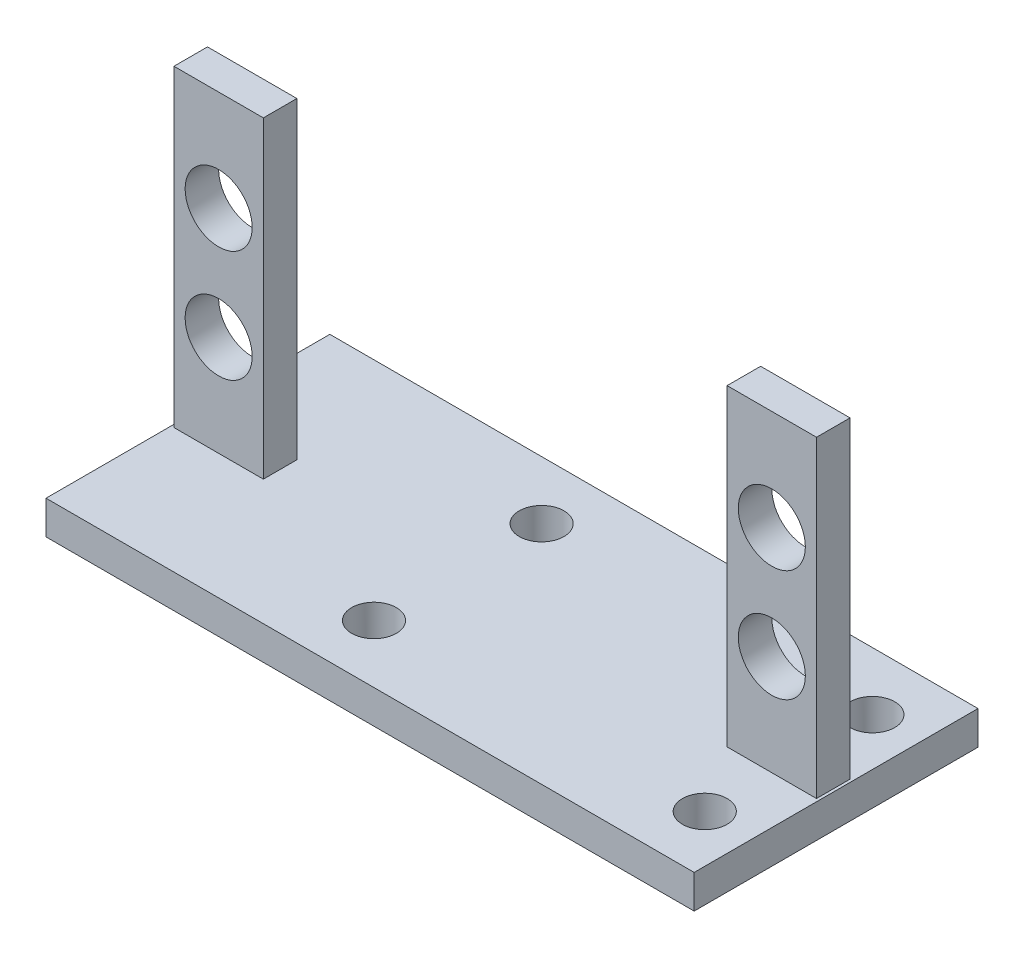
SolidWorks part; units mm, degrees
ref_plane "Front" through (0, 0, 0) normal (0, 0, 1) x (1, 0, 0)
ref_plane "Top" through (0, 0, 0) normal (0, 1, 0) x (1, 0, 0)
ref_plane "Right" through (0, 0, 0) normal (1, 0, 0) x (0, 0, -1)
sketch "草图1" plane through (0, 0, 0) normal (0, 1, 0) x (1, 0, 0)
  line L0 (0, 0) -> (0, 12.7) construction
  line L1 (0, 0) -> (0, -12.7) construction
  line L2 (0, 0) -> (29, 0) construction
  line L3 (-29, 12.7) -> (29, 12.7)
  line L4 (29, 12.7) -> (29, -12.7)
  line L5 (-29, 12.7) -> (-29, -12.7)
  line L6 (-29, -12.7) -> (29, -12.7)
  point P10 (-29, 0)
extrude "凸台-拉伸1" add sketch "草图1" along normal blind 3
sketch "草图2" plane through (0, 3, 0) normal (0, 1, 0) x (1, 0, 0)
  line L0 (0, 12.7) -> (24.75, 12.7) construction
  line L1 (29, 12.7) -> (-29, 12.7) construction
  line L2 (0, 12.7) -> (-24.75, 12.7) construction
  line L3 (-24.75, 12.7) -> (-24.75, 9.7) construction
  line L4 (-24.75, 9.7) -> (-28.75, 9.7) construction
  line L5 (-24.75, 9.7) -> (-20.75, 9.7) construction
  line L6 (24.75, 12.7) -> (24.75, 9.7) construction
  line L7 (24.75, 9.7) -> (28.75, 9.7) construction
  line L8 (24.75, 9.7) -> (20.75, 9.7) construction
  line L9 (-20.75, 9.7) -> (-28.75, 9.7)
  line L10 (-28.75, 9.7) -> (-28.75, 12.7)
  line L11 (-28.75, 12.7) -> (-20.75, 12.7)
  line L12 (-20.75, 12.7) -> (-20.75, 9.7)
  line L13 (20.75, 9.7) -> (28.75, 9.7)
  line L14 (28.75, 9.7) -> (28.75, 12.7)
  line L15 (28.75, 12.7) -> (20.75, 12.7)
  line L16 (20.75, 12.7) -> (20.75, 9.7)
  line L17 (-20.75, 0) -> (-20.75, 1.5) construction
  line L18 (-20.75, 1.5) -> (-28.75, 1.5) construction
  line L19 (-28.75, 1.5) -> (-28.75, -1.5) construction
  line L20 (-28.75, -1.5) -> (-20.75, -1.5) construction
  line L21 (-20.75, -1.5) -> (-20.75, 0) construction
  line L22 (0, 0) -> (0, 4.2412) construction
  line L23 (-28.75, 1.5) -> (-20.75, 1.5)
  line L24 (-20.75, 1.5) -> (-20.75, -1.5)
  line L25 (-20.75, -1.5) -> (-28.75, -1.5)
  line L26 (-28.75, -1.5) -> (-28.75, 1.5)
  line L27 (28.75, -1.5) -> (28.75, 1.5)
  line L28 (20.75, -1.5) -> (28.75, -1.5)
  line L29 (20.75, 1.5) -> (20.75, -1.5)
  line L30 (28.75, 1.5) -> (20.75, 1.5)
extrude "凸台-拉伸2" add sketch "草图2" along normal blind 28
sketch "草图3" plane through (0, 0, -9.7) normal (0, 0, 1) x (1, 0, 0)
  line L0 (-24.75, 17) -> (-20.75, 17) construction
  line L2 (-24.75, 17) -> (-24.75, 22) construction
  line L3 (-20.75, 31) -> (-20.75, 3) construction
  line L4 (-24.75, 17) -> (-24.75, 12) construction
  line L5 (0, 0) -> (0, 3) construction
  line L6 (-29, 3) -> (29, 3) construction
  circle A0 centre (-24.75, 12) radius 3
  circle A1 centre (-24.75, 22) radius 3
  circle A2 centre (24.75, 12) radius 3
  circle A3 centre (24.75, 22) radius 3
extrude "切除-拉伸1" cut sketch "草图3" against normal mid plane 24
sketch "草图4" plane through (0, 3, 0) normal (0, 1, 0) x (1, 0, 0)
  line L0 (0, 0) -> (24.75, 0) construction
  line L1 (24.75, 0) -> (24.75, 12.7) construction
  line L2 (28.75, 12.7) -> (20.75, 12.7) construction
  line L3 (24.75, 12.7) -> (9.95, 12.7) construction
  line L4 (20.75, 12.7) -> (-20.75, 12.7) construction
  line L5 (9.95, 12.7) -> (9.95, 0) construction
  line L6 (9.95, 0) -> (9.95, -12.7) construction
  line L7 (-29, -12.7) -> (29, -12.7) construction
  line L8 (9.95, 6.35) -> (-4.85, 6.35) construction
  line L9 (24.75, 0) -> (24.75, -7.5) construction
  circle A4 centre (24.75, -7.5) radius 2
  circle A5 centre (24.75, 7.5) radius 2
  circle A6 centre (-4.85, 7.5) radius 2
  circle A7 centre (-4.85, -7.5) radius 2
extrude "切除-拉伸2" cut sketch "草图4" against normal blind 22
sketch "草图5" plane through (0, 31, 0) normal (0, 1, 0) x (1, 0, 0)
  line L0 (-28.75, 12.7) -> (-28.75, 9.7)
  line L1 (-28.75, 9.7) -> (-20.75, 9.7)
  line L2 (-20.75, 9.7) -> (-20.75, 12.7)
  line L3 (-20.75, 12.7) -> (-28.75, 12.7)
  line L4 (20.75, 12.7) -> (20.75, 9.7)
  line L5 (20.75, 9.7) -> (28.75, 9.7)
  line L6 (28.75, 9.7) -> (28.75, 12.7)
  line L7 (28.75, 12.7) -> (20.75, 12.7)
extrude "切除-拉伸3" cut sketch "草图5" against normal blind 28
